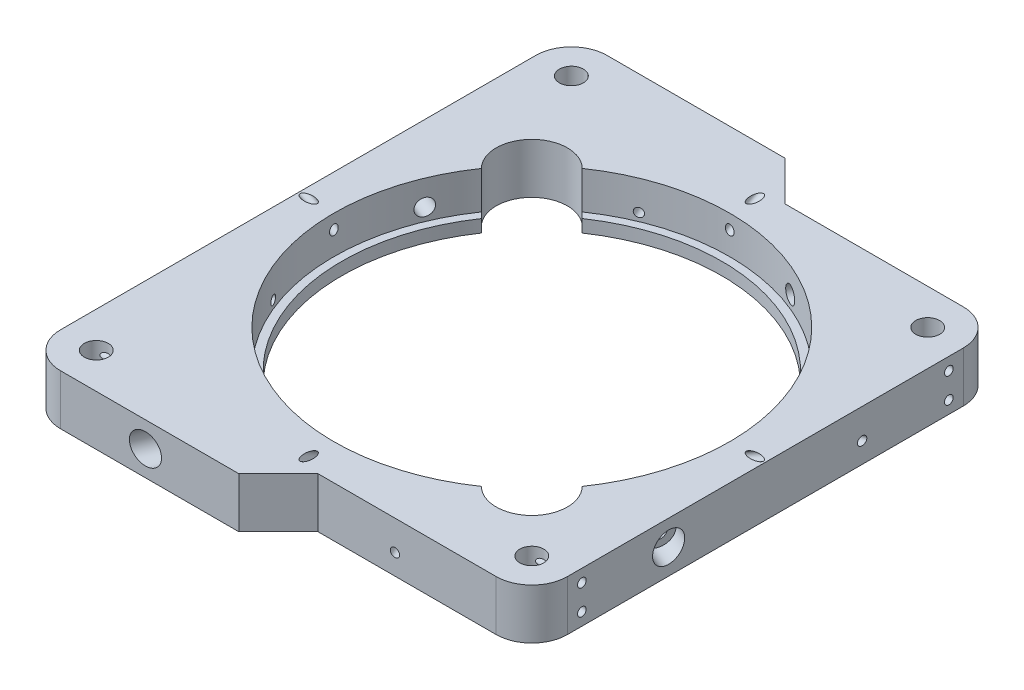
SolidWorks part; units mm, degrees
ref_plane "Front Plane" through (0, 0, 0) normal (0, 0, 1) x (1, 0, 0)
ref_plane "Top Plane" through (0, 0, 0) normal (0, 1, 0) x (1, 0, 0)
ref_plane "Right Plane" through (0, 0, 0) normal (1, 0, 0) x (0, 0, -1)
sketch "Sketch1" plane through (0, 0, 0) normal (0, 1, 0) x (1, 0, 0)
  line L0 (5, 59) -> (-5, 69)
  line L1 (-50, 50) -> (50, 50) construction
  line L4 (50, 50) -> (50, -50) construction
  line L5 (5, -59) -> (50, -59)
  line L6 (50, -50) -> (-50, -50) construction
  line L7 (-50, -50) -> (-50, 50) construction
  line L8 (59, 50) -> (59, -50)
  line L9 (-59, 59) -> (59, -59) construction
  line L10 (-59, -59) -> (59, 59) construction
  line L11 (-5, 69) -> (-50, 69)
  line L12 (-59, 60) -> (-59, -60)
  line L13 (-50, -69) -> (-5, -69)
  line L14 (-5, -69) -> (5, -59)
  line L15 (-50, 60) -> (-59, 69) construction
  line L16 (-59, -69) -> (-50, -60) construction
  line L17 (5, 59) -> (50, 59)
  circle A0 centre (50, 50) radius 3.025
  circle A1 centre (50, -50) radius 3.025
  circle A2 centre (-50, 60) radius 3.025
  circle A3 centre (-50, -60) radius 3.025
  arc A5 (50, -59) -> (59, -50) centre (50, -50) ccw
  arc A6 (50, 59) -> (59, 50) centre (50, 50) cw
  arc A8 (-59, -60) -> (-50, -69) centre (-50, -60) ccw
  arc A9 (-50, 69) -> (-59, 60) centre (-50, 60) ccw
  point P8 (50, 0)
  point P9 (0, 50)
  point P10 (0, 0)
  point P11 (-50, 0)
  point P12 (0, -50)
  point P34 (0, 64)
  point P39 (0, -64)
  dimension "D1" = 6.05
  dimension "D4" = 9
  dimension "D7" = 9
  dimension "D9" = 9
  dimension "D2" = 100
  dimension "D3" = 9
  dimension "D5" = 60
  dimension "D6" = 60
  dimension "D8" = 9
extrude "Boss-Extrude1" add sketch "Sketch1" along normal blind 12.7
sketch "Sketch2" plane through (59, 0, 0) normal (1, 0, 0) x (0, 0, -1)
  line L0 (46.35, 12.7) -> (46.975, 12.7) construction
  line L1 (46.35, 12.7) -> (46.35, 9.525) construction
  line L2 (-50, 12.7) -> (50, 12.7) construction
  line L3 (46.35, 9.525) -> (46.35, 3.175) construction
  line L4 (46.35, 3.175) -> (46.35, 0) construction
  line L5 (-50, 0) -> (50, 0) construction
  line L6 (-46.35, 12.7) -> (-46.35, 9.525) construction
  line L7 (-46.35, 9.525) -> (-46.35, 3.175) construction
  line L8 (-46.35, 3.175) -> (-46.35, 0) construction
  line L9 (-46.975, 12.7) -> (-46.35, 12.7) construction
  circle A0 centre (-46.35, 9.525) radius 1.095
  circle A1 centre (-46.35, 3.175) radius 1.095
  circle A2 centre (46.35, 9.525) radius 1.095
  circle A3 centre (46.35, 3.175) radius 1.095
  dimension "D1" = 2.19
  dimension "D2" = 3.175
  dimension "D3" = 0.625
extrude "Cut-Extrude1" cut sketch "Sketch2" against normal blind 15
sketch "Sketch4" plane through (0, 0, 0) normal (0, 0, 1) x (1, 0, 0)
  line L0 (0, 0) -> (0, 12.7)
  line L1 (5, 12.7) -> (50, 12.7) construction
  line L2 (0, 12.7) -> (50, 12.7)
  line L3 (50, 12.7) -> (50, 3.175)
  line L4 (50, 3.175) -> (48, 3.175)
  line L5 (48, 3.175) -> (48, 0)
  line L6 (5, 0) -> (50, 0) construction
  line L7 (48, 0) -> (0, 0)
  line L8 (-50, 12.7) -> (-5, 12.7) construction
  dimension "D1" = 2
  dimension "D2" = 50
  dimension "D3" = 9.525
revolve "Cut-Revolve1" cut sketch "Sketch4" angle 360 about L0
ref_axis "Axis1" through (0, 13.335, 0) along (0, -1, 0)
ref_plane "Plane1" through (0, 0, 0) normal (-0.3827, 0, 0.9239) x (0.9239, 0, 0.3827)
sketch "Sketch5" plane through (0, 0, 0) normal (-0.3827, 0, 0.9239) x (0.9239, 0, 0.3827)
  line L0 (0, 12.7) -> (0, 0) construction
  line L1 (0, 13.335) -> (0, -0.635) construction
  line L2 (27.1977, 12.7) -> (68.7723, 12.7) construction
  line L5 (27.1977, 0) -> (68.7723, 0) construction
  circle A0 centre (0, 6.35) radius 2.1
  point P10 (0, 6.35)
  dimension "D2" = 4.2
extrude "Cut-Extrude2" cut sketch "Sketch5" against normal through all
ref_plane "Plane2" through (0, 0, 0) normal (-0.9239, 0, 0.3827) x (0.3827, 0, 0.9239)
sketch "Sketch6" plane through (0, 0, 0) normal (-0.9239, 0, 0.3827) x (0.3827, 0, 0.9239)
  line L0 (-78.0111, 12.7) -> (32.8544, 12.7) construction
  line L1 (0, 12.7) -> (0, 3.175) construction
  line L3 (50, 12.7) -> (-50, 12.7) construction
  line L4 (50, 3.175) -> (-50, 3.175) construction
  line L5 (0, 13.335) -> (0, -0.635) construction
  circle A0 centre (0, 5.175) radius 1.095
  dimension "D1" = 2.19
  dimension "D2" = 2
extrude "Cut-Extrude3" cut sketch "Sketch6" against normal through all
ref_plane "Plane3" through (0, 0, 50) normal (0, 0, -1) x (-1, 0, 0)
ref_plane "Plane4" through (0, 25.5477, 44.25) normal (0, -0.5, -0.866) x (-1, 0, 0)
sketch "Sketch7" plane through (0, 25.5477, 44.25) normal (0, -0.5, -0.866) x (-1, 0, 0)
  line L0 (0, -14.0015) -> (0, -17.1765) construction
  line L1 (0, 11.5484) -> (0, -0.5499) construction
  circle A0 centre (0, -17.1765) radius 1.095
  ellipse E1 centre (0, 10.9985) end of major axis (-50, 10.9985) minor radius 25 construction
  dimension "D1" = 2.19
  dimension "D2" = 3.175
extrude "Cut-Extrude4" cut sketch "Sketch7" against normal up to surface and the other way up to surface up to face at (50, 12.7, 0) other way up to face at (45.7757, 5.4266, -20.1144)
pattern_circular "CirPattern1" count 4 over 360 about axis through (0, 13.335, 0) along (0, -1, 0) of "Cut-Extrude2", "Cut-Extrude3", "Cut-Extrude4"
sketch "Sketch8" plane through (0, 12.7, 0) normal (0, 1, 0) x (1, 0, 0)
  line L0 (-41.1418, 28.4139) -> (-39.7031, 26.9752)
  line L1 (-39.7031, 26.9752) -> (-26.9752, 39.7031)
  line L2 (-26.9752, 39.7031) -> (-28.4139, 41.1418)
  line L3 (0, 0) -> (-34.7779, 34.7779) construction
  line L4 (-34.7779, 34.7779) -> (-50, 50) construction
  line L5 (-59, 59) -> (59, -59) construction
  arc A0 (-41.1418, 28.4139) -> (-28.4139, 41.1418) centre (-34.7779, 34.7779) cw
  circle A1 centre (0, 0) radius 50 construction
  circle A2 centre (0, 0) radius 48 construction
  point P3 (-33.3392, 33.3392)
  dimension "D2" = 9
  dimension "D1" = 18
extrude "Cut-Extrude5" cut sketch "Sketch8" against normal through all
pattern_circular "CirPattern2" count 2 over 360 about axis through (0, 0, 0) along (0, 1, 0) of "Cut-Extrude5"
sketch "Sketch9" plane through (0, 0, 0) normal (-0.3827, 0, 0.9239) x (0.9239, 0, 0.3827)
  line L0 (0, 13.335) -> (0, -0.635) construction
  circle A0 centre (0, 6.35) radius 3.75
  circle A1 centre (0, 6.35) radius 2.1 construction
  dimension "D1" = 7.5
extrude "Cut-Extrude6" cut sketch "Sketch9" along normal blind 5 and the other way through all from offset 63.3333
pattern_circular "CirPattern6" count 4 over 360 about axis through (0, 0, 0) along (0, 1, 0) of "Cut-Extrude6"
sketch "Sketch10" plane through (-59, 0, 0) normal (-1, 0, 0) x (0, 0, 1)
  line L0 (-56.35, 9.525) -> (-60, 9.525) construction
  line L1 (-60, 12.7) -> (-60, 0) construction
  line L3 (56.35, 9.525) -> (60, 9.525) construction
  line L4 (60, 12.7) -> (60, 0) construction
  circle A0 centre (56.35, 9.525) radius 1.095
  circle A1 centre (56.35, 3.175) radius 1.095
  circle A2 centre (-56.35, 9.525) radius 1.095
  circle A3 centre (-56.35, 3.175) radius 1.095
  circle A5 centre (-46.35, 3.175) radius 1.095 construction
  dimension "D1" = 0.625
extrude "Cut-Extrude7" cut sketch "Sketch10" against normal blind 15
